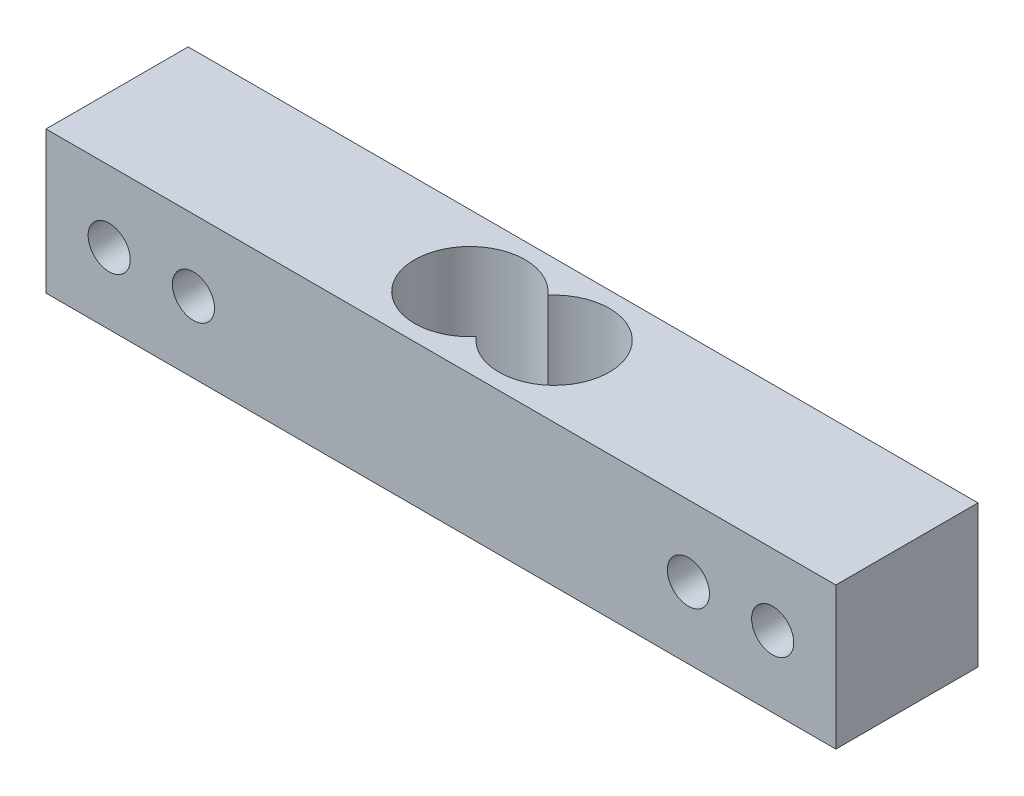
SolidWorks part; units mm, degrees
ref_plane "Front Plane" through (0, 0, 0) normal (0, 0, 1) x (1, 0, 0)
ref_plane "Top Plane" through (0, 0, 0) normal (0, 1, 0) x (1, 0, 0)
ref_plane "Right Plane" through (0, 0, 0) normal (1, 0, 0) x (0, 0, -1)
sketch "Sketch1" plane through (0, 0, 0) normal (0, 0, 1) x (1, 0, 0)
  line L0 (0, 0) -> (75, 0)
  line L1 (75, 0) -> (75, 13.5)
  line L2 (75, 13.5) -> (0, 13.5)
  line L3 (0, 13.5) -> (0, 0)
  line L4 (0, 6.75) -> (6, 6.75) construction
  line L5 (6, 6.75) -> (14, 6.75) construction
  line L6 (75, 6.75) -> (69, 6.75) construction
  line L8 (69, 6.75) -> (61, 6.75) construction
  circle A0 centre (6, 6.75) radius 2
  circle A1 centre (14, 6.75) radius 2
  circle A2 centre (69, 6.75) radius 2
  circle A3 centre (61, 6.75) radius 2
sketch "Sketch2" plane through (0, 0, 0) normal (0, 0, 1) x (1, 0, 0)
  line L0 (0, 0) -> (75, 0)
  line L1 (75, 0) -> (75, 13.5)
  line L2 (75, 13.5) -> (0, 13.5)
  line L3 (0, 13.5) -> (0, 0)
  line L4 (0, 6.75) -> (6, 6.75) construction
  line L5 (6, 6.75) -> (14, 6.75) construction
  line L6 (75, 6.75) -> (69, 6.75) construction
  line L7 (69, 6.75) -> (61, 6.75) construction
  circle A0 centre (6, 6.75) radius 2
  circle A1 centre (14, 6.75) radius 2
  circle A2 centre (69, 6.75) radius 2
  circle A3 centre (61, 6.75) radius 2
extrude "Boss-Extrude1" add sketch "Sketch2" along normal blind 13.5
sketch "Sketch3" plane through (0, 13.5, 0) normal (0, 1, 0) x (1, 0, 0)
  line L0 (37.5, -13.5) -> (37.5, 0) construction
  line L1 (75, -13.5) -> (0, -13.5) construction
  line L2 (0, 0) -> (75, 0) construction
  line L3 (37.5, -6.75) -> (33.5, -6.75) construction
  line L4 (37.5, -6.75) -> (41.5, -6.75) construction
  arc A0 (37.5, -3.3496) -> (37.5, -10.1504) centre (33.5, -6.75) ccw
  arc A1 (37.5, -10.1504) -> (37.5, -3.3496) centre (41.5, -6.75) ccw
extrude "Cut-Extrude1" cut sketch "Sketch3" against normal blind 13.5
ref_plane "sensor-fix-1" through (6, 0, 0) normal (-1, 0, 0) x (0, 0, 1)
ref_plane "sensor-fix-2" through (0, 6.75, 0) normal (0, -1, 0) x (-1, 0, 0)
